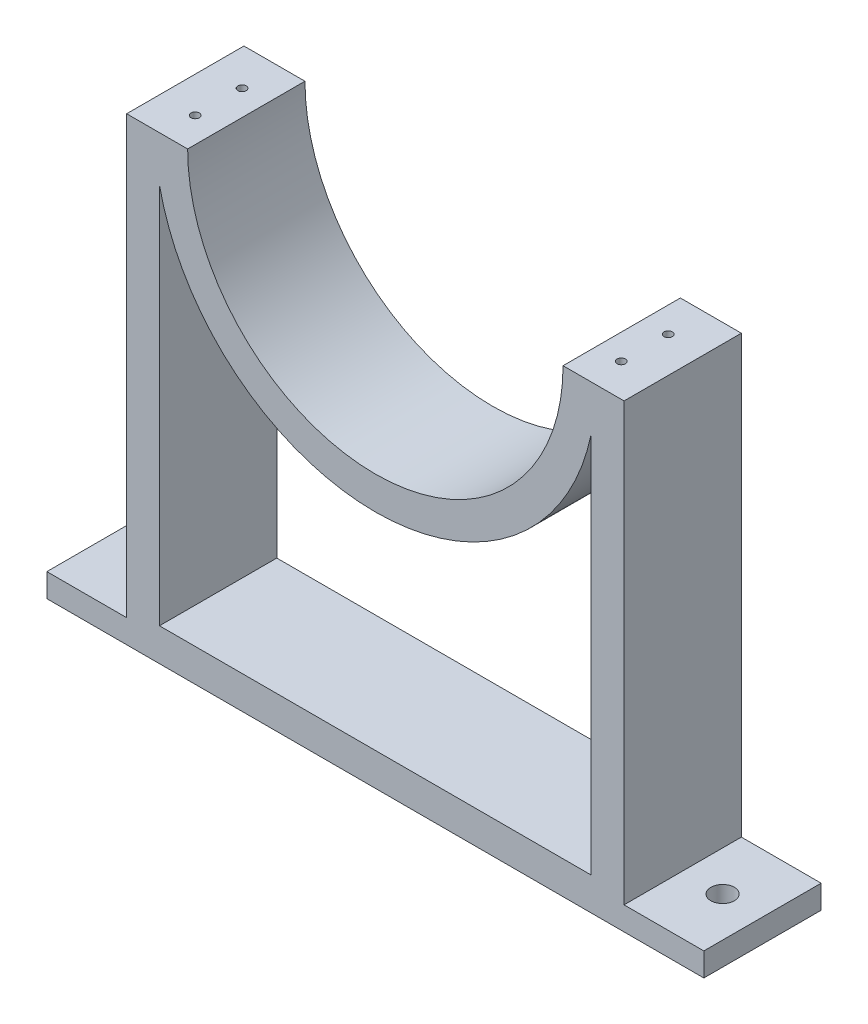
SolidWorks part; units mm, degrees
material "ABS"
ref_plane "Front Plane" through (0, 0, 0) normal (0, 0, 1) x (1, 0, 0)
ref_plane "Top Plane" through (0, 0, 0) normal (0, 1, 0) x (1, 0, 0)
ref_plane "Right Plane" through (0, 0, 0) normal (1, 0, 0) x (0, 0, -1)
sketch "Sketch1" plane through (0, 0, 0) normal (0, 0, 1) x (1, 0, 0)
  line L0 (0, 58.8561) -> (0, -54.5821) construction
  line L1 (-50.8, 0) -> (-67.31, 0)
  line L2 (-67.31, 0) -> (-67.31, -118.11)
  line L3 (-67.31, -118.11) -> (-88.9, -118.11)
  line L4 (-88.9, -118.11) -> (-88.9, -124.46)
  line L5 (-88.9, -124.46) -> (88.9, -124.46)
  line L6 (0, -124.46) -> (0, -46.0375)
  line L7 (88.9, -118.11) -> (88.9, -124.46)
  line L8 (67.31, -118.11) -> (88.9, -118.11)
  line L9 (67.31, 0) -> (67.31, -118.11)
  line L10 (50.8, 0) -> (67.31, 0)
  arc A0 (-50.8, 0) -> (50.8, 0) centre (0, 0) ccw
  dimension "D5" = 50.8
  dimension "D1" = 88.9
  dimension "D2" = 6.35
  dimension "D3" = 124.46
  dimension "D4" = 16.51
extrude "Boss-Extrude1" add sketch "Sketch1" along normal mid plane 31.75 contours A0 L1 L2 L3 L4 L5 L6 | A0 L6 L5 L7 L8 L9 L10
shell "Shell1" thickness 8.89
sketch "Sketch2" plane through (0, -118.11, 0) normal (0, 1, 0) x (1, 0, 0)
  line L0 (-67.31, -15.875) -> (-88.9, -15.875) construction
  line L1 (-88.9, -15.875) -> (-88.9, 15.875) construction
  line L2 (0, -25.3383) -> (0, 37.3952) construction
  circle A0 centre (-78.105, 0) radius 3.175
  circle A1 centre (78.105, 0) radius 3.175
  point P5 (-78.105, -15.875)
  point P9 (-88.9, 0)
  dimension "D1" = 6.35
extrude "Cut-Extrude1" cut sketch "Sketch2" against normal through all
sketch "Sketch3" plane through (0, 0, 0) normal (0, 1, 0) x (1, 0, 0)
  line L0 (-50.8, -15.875) -> (-50.8, 15.875) construction
  line L1 (-50.8, -15.875) -> (-67.31, -15.875) construction
  line L2 (0, 27.9758) -> (0, -35.6997) construction
  circle A0 centre (-57.658, 5.715) radius 1.905
  circle A1 centre (-57.658, -6.985) radius 1.905
  circle A2 centre (57.658, -6.985) radius 1.905
  circle A3 centre (57.658, 5.715) radius 1.905
  dimension "D1" = 3.81
  dimension "D2" = 12.7
  dimension "D3" = 6.858
  dimension "D4" = 8.89
hole_wizard "#4-40 Tapped Hole1" positions "Sketch4" profile "Sketch5" tap size "#4-40" standard "ANSI Inch"
sketch "Sketch4" plane through (0, 0, 0) normal (0, 1, 0) x (1, 0, 0)
  point P0 (-57.658, 5.715)
  point P3 (-57.658, -6.985)
  point P6 (57.658, -6.985)
  point P9 (57.658, 5.715)
sketch "Sketch5" plane through (-57.658, 0, -5.715) normal (1, 0, 0) x (0, 0, 1)
  line L0 (0, 0) -> (0, 8.2992)
  line L1 (0, 8.2992) -> (1.1303, 7.62)
  line L2 (1.1303, 7.62) -> (1.1303, 0)
  line L5 (1.1303, 0) -> (0, 0)
  line L10 (0, 8.2992) -> (-1.1303, 7.62) construction
  line L11 (0, -6.35) -> (0, 107.95) construction
  dimension "Tap Drill Dia." = 2.2606
  dimension "Tap Drill Depth" = 7.62
  dimension "Drill Angle" = 118
cosmetic thread "Hole Thread1" parameters "D1"=5.588, "D2"=2.8448
cosmetic thread "Hole Thread2" parameters "D1"=5.588, "D2"=2.8448
cosmetic thread "Hole Thread3" parameters "D1"=5.588, "D2"=2.8448
cosmetic thread "Hole Thread4" parameters "D1"=5.588, "D2"=2.8448
